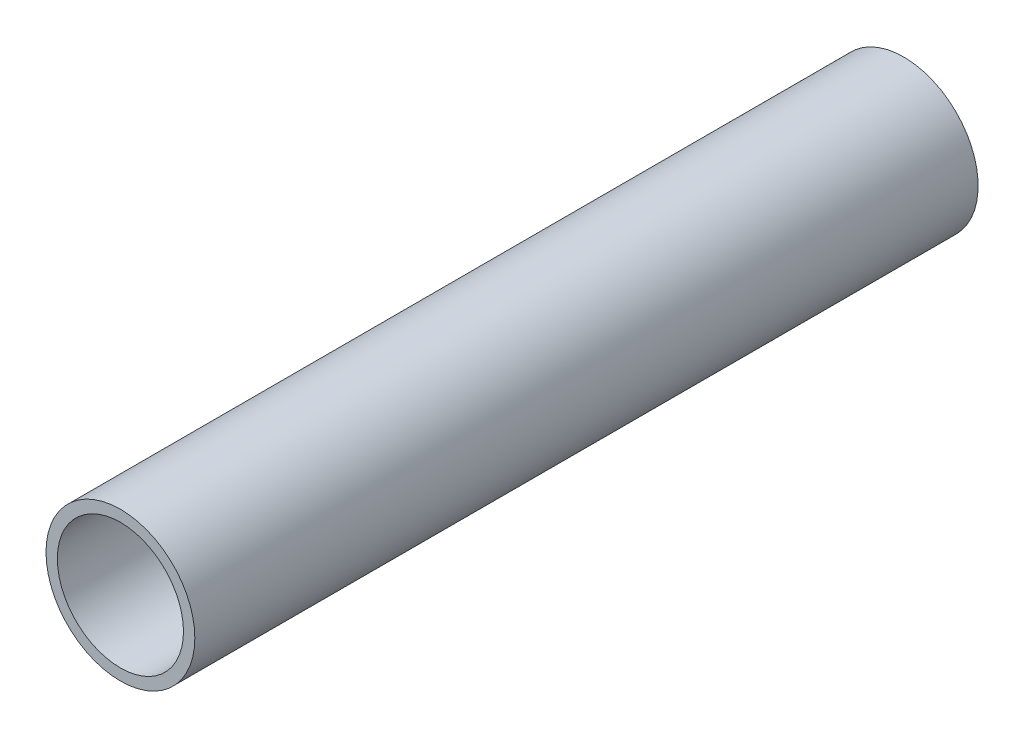
SolidWorks part; units mm, degrees
ref_plane "Front Plane" through (0, 0, 0) normal (0, 0, 1) x (1, 0, 0)
ref_plane "Top Plane" through (0, 0, 0) normal (0, 1, 0) x (1, 0, 0)
ref_plane "Right Plane" through (0, 0, 0) normal (1, 0, 0) x (0, 0, -1)
ref_plane "Plane1" through (0, 0, 0) normal (0, -1, 0) x (1, 0, 0)
sketch "Sketch1" plane through (0, 0, 0) normal (0, -1, 0) x (1, 0, 0)
  line L0 (24.13, 762) -> (20.447, 762)
  line L1 (20.447, 762) -> (20.447, -762)
  line L2 (20.447, -762) -> (24.13, -762)
  line L3 (24.13, -762) -> (24.13, 762)
  line L4 (0, 762) -> (0, -762) construction
revolve "Revolve1" add sketch "Sketch1" angle 360 about L4
sketch "Sketch2" plane through (0, 0, 762) normal (0, 0, 1) x (1, 0, 0)
  circle A0 centre (0, 0) radius 33.6553
extrude "Cut-Extrude1" cut sketch "Sketch2" against normal blind 1270
